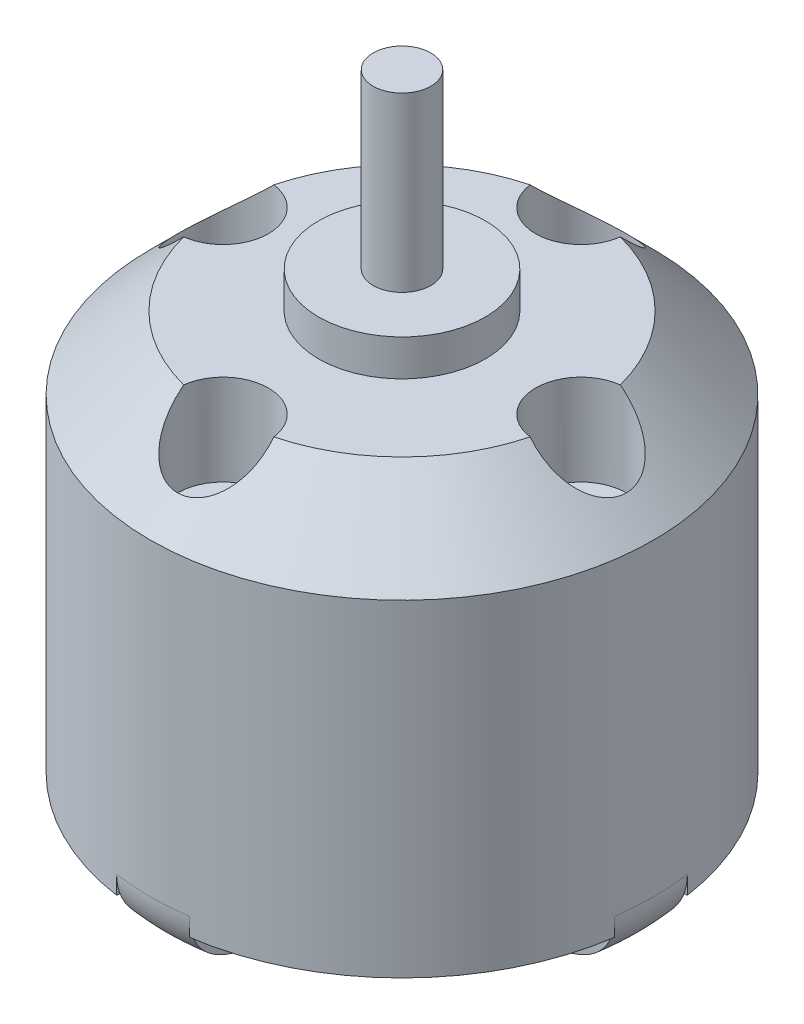
SolidWorks part; units mm, degrees
ref_plane "Front Plane" through (0, 0, 0) normal (0, 0, 1) x (1, 0, 0)
ref_plane "Top Plane" through (0, 0, 0) normal (0, 1, 0) x (1, 0, 0)
ref_plane "Right Plane" through (0, 0, 0) normal (1, 0, 0) x (0, 0, -1)
sketch "Sketch1" plane through (0, 0, 0) normal (0, 1, 0) x (1, 0, 0)
  circle A0 centre (0, 0) radius 13.85
  dimension "D1" = 27.7
extrude "Boss-Extrude1" add sketch "Sketch1" along normal blind 26
sketch "Sketch2" plane through (0, 26, 0) normal (0, 1, 0) x (-1, 0, 0)
  circle A0 centre (0, 0) radius 4.5875
  circle A1 centre (0, 0) radius 13.85
  dimension "D1" = 9.175
extrude "Cut-Extrude1" cut sketch "Sketch2" against normal blind 2
sketch "Sketch3" plane through (0, 26, 0) normal (0, 1, 0) x (1, 0, 0)
  circle A0 centre (0, 0) radius 1.5875
  dimension "D1" = 3.175
extrude "Boss-Extrude2" add sketch "Sketch3" along normal blind 9.5
chamfer "Chamfer1" distance 4 angle 45 1 edges at (0, 24, 13.85)
sketch "Sketch5" plane through (0, 24, 0) normal (0, 1, 0) x (1, 0, 0)
  circle A0 centre (-9.85, 0) radius 2.5
  circle A1 centre (0, 0) radius 9.85 construction
  circle A2 centre (0, 9.85) radius 2.5
  circle A3 centre (9.85, 0) radius 2.5
  circle A4 centre (0, -9.85) radius 2.5
  dimension "D1" = 5
  dimension "D2" = 5
  dimension "D3" = 5
  dimension "D4" = 5
extrude "Cut-Extrude2" cut sketch "Sketch5" against normal blind 5
sketch "Sketch6" plane through (0, 0, 0) normal (0, -1, 0) x (1, 0, 0)
  circle A0 centre (0, -8) radius 0.8
  circle A1 centre (9.5, 0) radius 0.8
  circle A2 centre (0, 8) radius 0.8
  circle A3 centre (-9.5, 0) radius 0.8
  dimension "D1" = 1.6
  dimension "D2" = 1.6
  dimension "D3" = 1.6
  dimension "D4" = 1.6
  dimension "D5" = 19
  dimension "D6" = 16
  dimension "D7" = 8
  dimension "D8" = 9.5
extrude "Cut-Extrude3" cut sketch "Sketch6" against normal blind 5
fillet "Fillet1" radius 3 1 edges at (0, 0, 13.85)
sketch "Sketch7" plane through (0, 0, 0) normal (0, 1, 0) x (1, 0, 0)
  arc A0 (-13.7048, 2) -> (-2, 13.7048) centre (-12.6687, 12.6687) ccw
  circle A1 centre (0, 0) radius 13.85 construction
  arc A2 (-13.7048, -2) -> (-2, -13.7048) centre (0, 0) ccw
  arc A3 (2, -13.7048) -> (13.7048, -2) centre (0, 0) ccw
  arc A4 (13.7048, 2) -> (2, 13.7048) centre (0, 0) ccw
  arc A5 (13.7048, 2) -> (2, 13.7048) centre (12.6687, 12.6687) cw
  arc A6 (-2, 13.7048) -> (-13.7048, 2) centre (0, 0) ccw
  arc A7 (13.7048, -2) -> (2, -13.7048) centre (12.6687, -12.6687) ccw
  arc A9 (-13.7048, -2) -> (-2, -13.7048) centre (-12.6687, -12.6687) cw
  point P6 (0, 0)
extrude "Cut-Extrude4" cut sketch "Sketch7" along normal blind 3
sketch "Sketch10" plane through (0, 3, 0) normal (0, -1, 0) x (1, 0, 0)
  arc A0 (-2, 13.7048) -> (-13.7048, 2) centre (0, 0) ccw
  arc A1 (-1.9499, 12.7012) -> (-12.7012, 1.9499) centre (0, 0) ccw
  arc A2 (-2, 13.7048) -> (-1.9499, 12.7012) centre (-12.6687, 12.6687) cw
  arc A3 (2, 13.7048) -> (1.9499, 12.7012) centre (12.6687, 12.6687) ccw
  arc A4 (13.7048, -2) -> (12.7012, -1.9499) centre (12.6687, -12.6687) ccw
  arc A5 (-2, -13.7048) -> (-1.9499, -12.7012) centre (-12.6687, -12.6687) ccw
  arc A6 (12.7012, 1.9499) -> (13.7048, 2) centre (12.6687, 12.6687) ccw
  arc A7 (1.9499, -12.7012) -> (2, -13.7048) centre (12.6687, -12.6687) ccw
  arc A8 (-12.7012, -1.9499) -> (-13.7048, -2) centre (-12.6687, -12.6687) ccw
  arc A9 (-12.7012, 1.9499) -> (-13.7048, 2) centre (-12.6687, 12.6687) cw
  arc A10 (-12.7012, -1.9499) -> (-1.9499, -12.7012) centre (0, 0) ccw
  arc A11 (-13.7048, -2) -> (-2, -13.7048) centre (0, 0) ccw
  arc A12 (12.7012, 1.9499) -> (1.9499, 12.7012) centre (0, 0) ccw
  arc A13 (13.7048, 2) -> (2, 13.7048) centre (0, 0) ccw
  arc A14 (2, -13.7048) -> (13.7048, -2) centre (0, 0) ccw
  arc A15 (1.9499, -12.7012) -> (12.7012, -1.9499) centre (0, 0) ccw
  dimension "D1" = 25.7
extrude "Boss-Extrude3" add sketch "Sketch10" along normal blind 1
sketch "Sketch11" plane through (0, 0, 0) normal (0, -1, 0) x (1, 0, 0)
  circle A0 centre (0, 0) radius 3.5
  dimension "D1" = 7
extrude "Boss-Extrude4" add sketch "Sketch11" along normal blind 0.5
sketch "Sketch12" plane through (0, -0.5, 0) normal (0, -1, 0) x (1, 0, 0)
  circle A0 centre (0, 0) radius 1.5875
  dimension "D1" = 3.175
extrude "Boss-Extrude5" add sketch "Sketch12" along normal blind 1
sketch "Sketch13" plane through (0, 0, 0) normal (0, -1, 0) x (1, 0, 0)
  circle A0 centre (9.5, 0) radius 1.25
  circle A1 centre (0, -8) radius 1.25
  circle A2 centre (-9.5, 0) radius 1.25
  circle A3 centre (0, 8) radius 1.25
  dimension "D1" = 2.5
  dimension "D2" = 2.5
  dimension "D3" = 2.5
  dimension "D4" = 2.5
extrude "Cut-Extrude5" cut sketch "Sketch13" against normal blind 5
